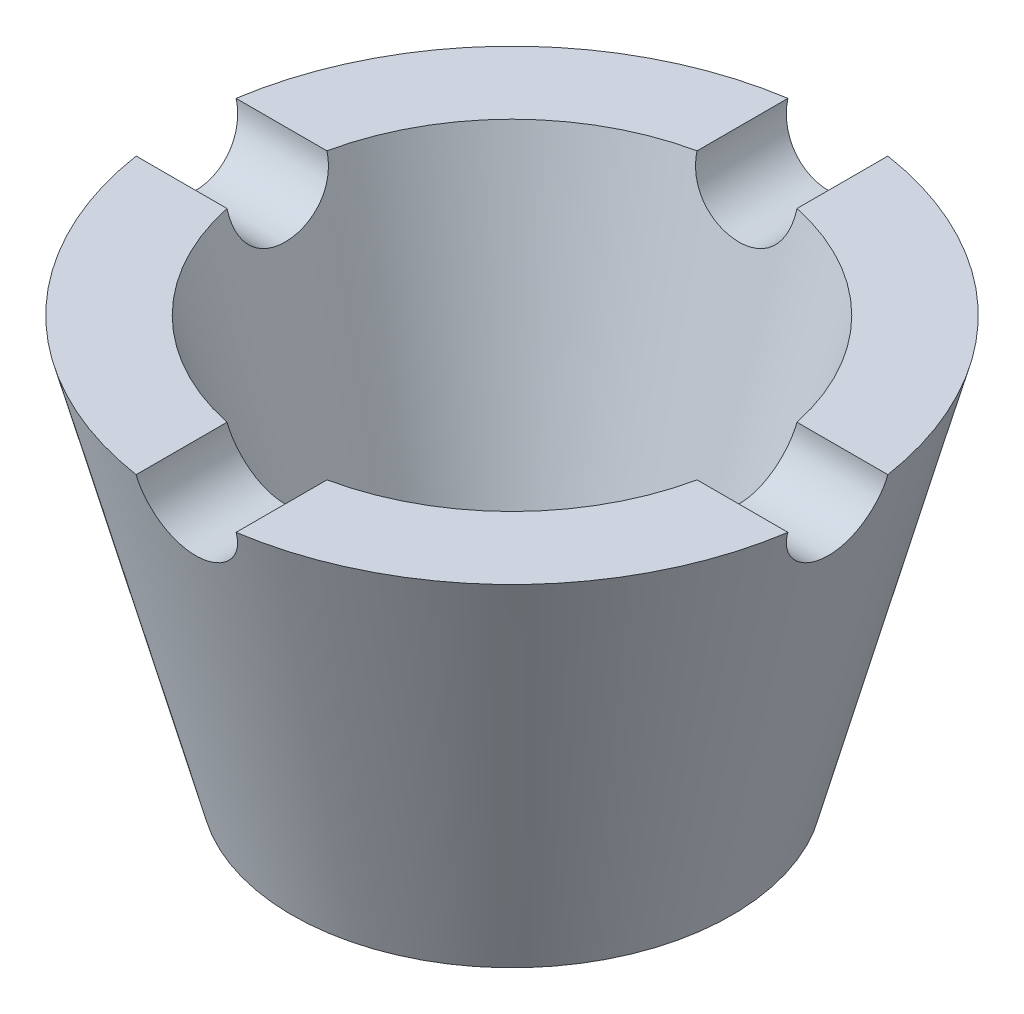
SolidWorks part; units mm, degrees
ref_plane "Front Plane" through (0, 0, 0) normal (0, 0, 1) x (1, 0, 0)
ref_plane "Top Plane" through (0, 0, 0) normal (0, 1, 0) x (1, 0, 0)
ref_plane "Right Plane" through (0, 0, 0) normal (1, 0, 0) x (0, 0, -1)
sketch "Sketch1" plane through (0, 0, 0) normal (0, 0, 1) x (1, 0, 0)
  line L0 (-11, 0) -> (-22, 0)
  line L1 (-11, 0) -> (-11, 11)
  line L2 (0, 0) -> (0, 51.2962) construction
  line L3 (-11, 11) -> (-16, 11)
  line L4 (-24.0488, 41) -> (-33, 41)
  line L5 (-22, 0) -> (-33, 41)
  line L6 (-16, 11) -> (-24.0488, 41)
  dimension "D1" = 22
  dimension "D2" = 11
  dimension "D3" = 24.0488
  dimension "D4" = 11
  dimension "D5" = 41
  dimension "D6" = 16
  dimension "D7" = 11
revolve "Revolve1" add sketch "Sketch1" angle 360 about L2
sketch "Sketch2" plane through (0, 0, 0) normal (0, 0, 1) x (1, 0, 0)
  line L0 (0, 0) -> (0, 45.5779) construction
  line L2 (-5, 41) -> (5, 41)
  arc A0 (-5, 41) -> (5, 41) centre (0, 41) ccw
  dimension "D1" = 10
  dimension "D4" = 41
extrude "Cut-Extrude1" cut sketch "Sketch2" against normal through all both and the other way through all
sketch "Sketch3" plane through (0, 0, 0) normal (1, 0, 0) x (0, 0, -1)
  line L0 (32.619, 41) -> (-32.619, 41) construction
  line L1 (-5, 41) -> (5, 41)
  arc A0 (-5, 41) -> (5, 41) centre (0, 41) ccw
  dimension "D1" = 10
extrude "Cut-Extrude2" cut sketch "Sketch3" against normal through all both and the other way through all
